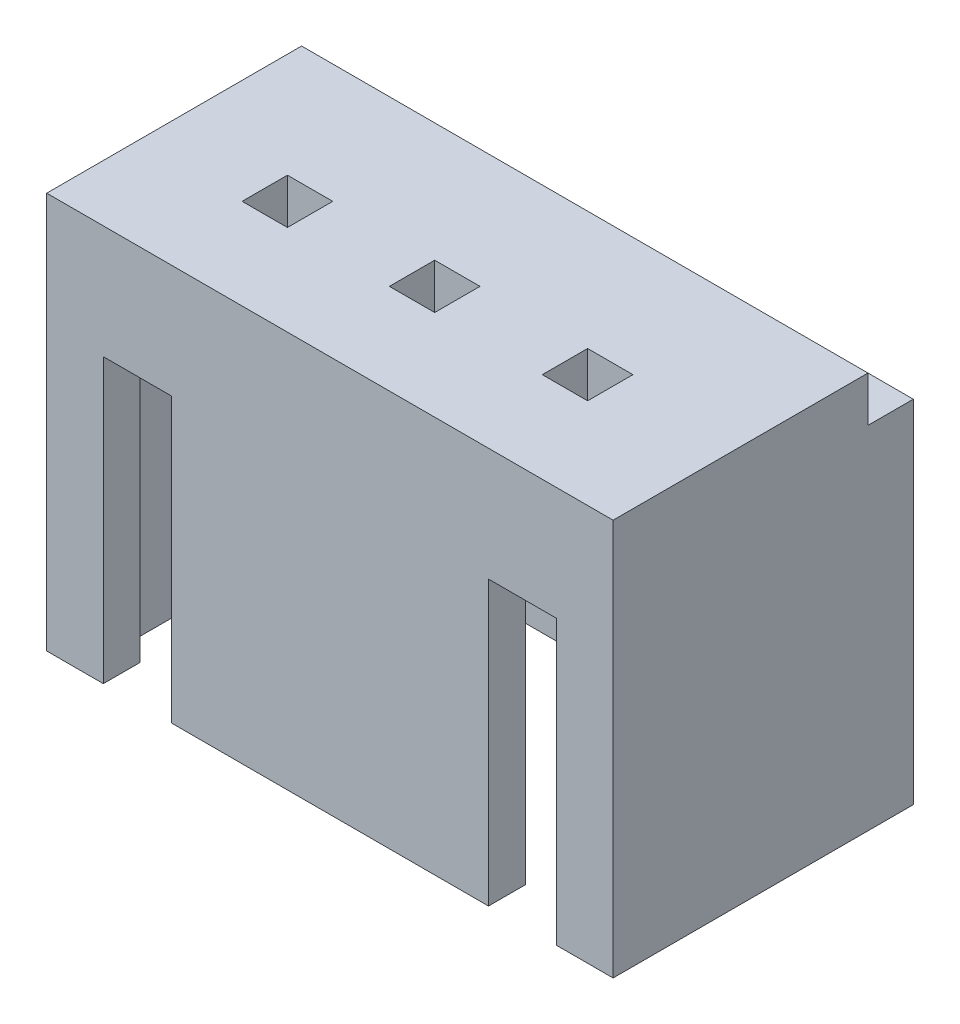
SolidWorks part; units mm, degrees
ref_plane "Front Plane" through (0, 0, 0) normal (0, 0, 1) x (1, 0, 0)
ref_plane "Top Plane" through (0, 0, 0) normal (0, 1, 0) x (1, 0, 0)
ref_plane "Right Plane" through (0, 0, 0) normal (1, 0, 0) x (0, 0, -1)
sketch "Sketch1" plane through (0, 0, 0) normal (0, 1, 0) x (1, 0, 0)
  line L1 (-5, -2.65) -> (5, -2.65)
  line L2 (-5, -2.65) -> (-5, 2.65)
  line L3 (-5, 2.65) -> (5, 2.65)
  line L4 (5, -2.65) -> (5, 2.65)
  line L5 (-5, -2.65) -> (5, 2.65) construction
  line L6 (-5, 2.65) -> (5, -2.65) construction
  point P0 (0, 0)
  dimension "D1" = 10
  dimension "D2" = 5.3
extrude "Boss-Extrude1" add sketch "Sketch1" along normal blind 7
sketch "Sketch3" plane through (0, 0, 0) normal (0, -1, 0) x (1, 0, 0)
  line L1 (-4.4, -2) -> (4.4, -2)
  line L2 (-4.4, -2) -> (-4.4, 2)
  line L3 (-4.4, 2) -> (4.4, 2)
  line L4 (4.4, -2) -> (4.4, 2)
  line L5 (-4.4, -2) -> (4.4, 2) construction
  line L6 (-4.4, 2) -> (4.4, -2) construction
  point P0 (0, 0)
  dimension "D1" = 8.8
  dimension "D2" = 4
extrude "Cut-Extrude1" cut sketch "Sketch3" against normal blind 5
sketch "Sketch4" plane through (0, 0, 2.65) normal (0, 0, 1) x (1, 0, 0)
  line L0 (-5, 0) -> (5, 0) construction
  line L1 (-4, 0) -> (-2.8, 0)
  line L2 (-4, 0) -> (-4, 5)
  line L3 (-4, 5) -> (-2.8, 5)
  line L4 (-2.8, 0) -> (-2.8, 5)
  line L6 (2.8, 0) -> (4, 0)
  line L7 (2.8, 0) -> (2.8, 5)
  line L8 (2.8, 5) -> (4, 5)
  line L9 (4, 0) -> (4, 5)
  dimension "D1" = 1.2
  dimension "D2" = 1.2
  dimension "D3" = 4
  dimension "D4" = 8
  dimension "D5" = 5
extrude "Cut-Extrude2" cut sketch "Sketch4" against normal blind 4
sketch "Sketch5" plane through (0, 7, 0) normal (0, 1, 0) x (1, 0, 0)
  line L0 (5, -2.65) -> (5, 2.65) construction
  line L1 (5, 1.85) -> (-5, 1.85)
  line L2 (5, 1.85) -> (5, 2.65)
  line L3 (5, 2.65) -> (-5, 2.65)
  line L4 (-5, 1.85) -> (-5, 2.65)
  dimension "D1" = 0.8
extrude "Cut-Extrude3" cut sketch "Sketch5" against normal blind 0.8 contours L1 L4 L3 L2
sketch "Sketch6" plane through (0, 7, 0) normal (0, 1, 0) x (1, 0, 0)
  line L2 (2.95, -1.05) -> (2.15, -1.05)
  line L3 (2.95, -1.05) -> (2.95, -0.25)
  line L4 (2.95, -0.25) -> (2.15, -0.25)
  line L6 (2.15, -1.05) -> (2.15, -0.25)
  line L7 (0.25, -1.05) -> (-0.55, -1.05)
  line L8 (0.25, -1.05) -> (0.25, -0.25)
  line L9 (0.25, -0.25) -> (-0.55, -0.25)
  line L11 (-0.55, -1.05) -> (-0.55, -0.25)
  line L12 (-2.35, -1.05) -> (-3.15, -1.05)
  line L13 (-2.35, -1.05) -> (-2.35, -0.25)
  line L14 (-2.35, -0.25) -> (-3.15, -0.25)
  line L15 (-3.15, -1.05) -> (-3.15, -0.25)
extrude "Cut-Extrude4" cut sketch "Sketch6" against normal blind 10
sketch "Sketch7" plane through (0, 5, 0) normal (0, -1, 0) x (1, 0, 0)
  line L0 (4.4, -2) -> (4.4, 2) construction
  line L1 (-4.4, -2) -> (4.4, -2)
  line L2 (-4.4, -2) -> (-4.4, -1)
  line L3 (-4.4, -1) -> (4.4, -1)
  line L4 (4.4, -2) -> (4.4, -1)
  dimension "D1" = 1
extrude "Cut-Extrude5" cut sketch "Sketch7" against normal blind 0.3
